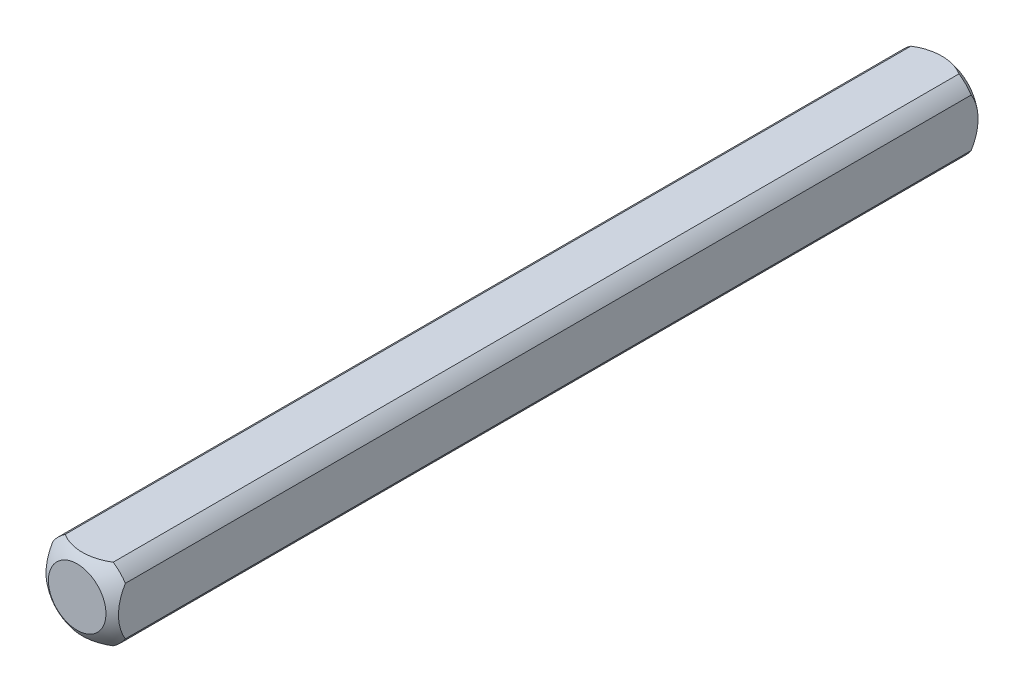
SolidWorks part; units mm, degrees
material "Custom Plastic"
ref_plane "Front Plane" through (0, 0, 0) normal (0, 0, 1) x (1, 0, 0)
ref_plane "Top Plane" through (0, 0, 0) normal (0, 1, 0) x (1, 0, 0)
ref_plane "Right Plane" through (0, 0, 0) normal (1, 0, 0) x (0, 0, -1)
sketch "Sketch1" plane through (0, 0, 0) normal (0, 0, 1) x (1, 0, 0)
  line L0 (-3.175, -3.175) -> (3.175, 3.175) construction
  line L1 (-3.175, -3.175) -> (3.175, -3.175)
  line L2 (-3.175, -3.175) -> (-3.175, 3.175)
  line L3 (-3.175, 3.175) -> (3.175, 3.175)
  line L4 (3.175, -3.175) -> (3.175, 3.175)
  dimension "D1" = 6.35
extrude "Boss-Extrude1" add sketch "Sketch1" along normal blind 38.1
sketch "Sketch2" plane through (0, 0, 0) normal (0, 0, -1) x (-1, 0, 0)
  circle A0 centre (0, 0) radius 3.81
  dimension "D1" = 7.62
extrude "Cut-Extrude1" cut sketch "Sketch2" against normal through all flip side to cut
ref_axis "Axis1" through (0, 0, 38.1) along (0, 0, -1)
sketch "Sketch3" plane through (0, 0, 0) normal (0, 1, 0) x (1, 0, 0)
  line L1 (-5.0537, -3.8933) -> (-5.0537, 5.7405)
  line L2 (-5.0537, 5.7405) -> (0, 5.7405)
  line L5 (0, -38.1) -> (0, 0) construction
  line L8 (0, 0.6703) -> (0, 5.7405)
  arc A0 (-5.0537, -3.8933) -> (0, 0.6703) centre (0, -4.4097) cw
  dimension "D1" = 5.08
revolve "Cut-Revolve1" cut sketch "Sketch3" angle 360 about axis through (0, 0, 38.1) along (0, 0, -1)
mirror "Mirror1" about plane through (0, 0, 38.1) normal (0, 0, -1) of bodies 103
